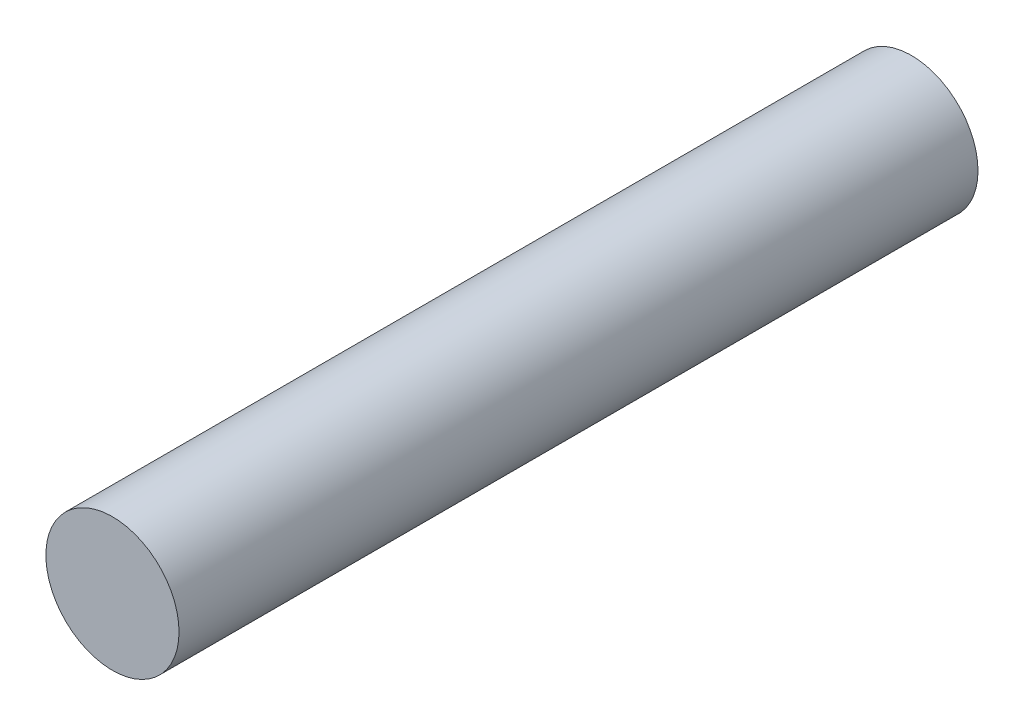
SolidWorks part; units mm, degrees
ref_plane "Front Plane" through (0, 0, 0) normal (0, 0, 1) x (1, 0, 0)
ref_plane "Top Plane" through (0, 0, 0) normal (0, 1, 0) x (1, 0, 0)
ref_plane "Right Plane" through (0, 0, 0) normal (1, 0, 0) x (0, 0, -1)
sketch "Sketch1" plane through (0, 0, 0) normal (0, 0, 1) x (1, 0, 0)
  circle A0 centre (0, 0) radius 635
  dimension "D1" = 1270
extrude "Boss-Extrude1" add sketch "Sketch1" along normal mid plane 7620
equation "\"fl\"=2.1327"
